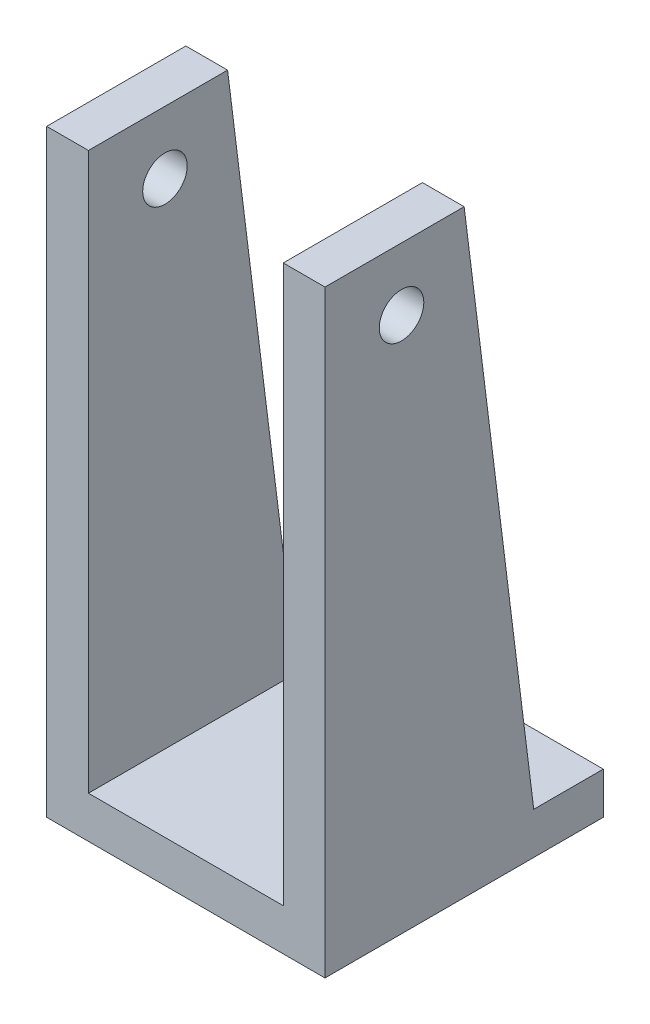
SolidWorks part; units mm, degrees
ref_plane "前视基准面" through (0, 0, 0) normal (0, 0, 1) x (1, 0, 0)
ref_plane "上视基准面" through (0, 0, 0) normal (0, 1, 0) x (1, 0, 0)
ref_plane "右视基准面" through (0, 0, 0) normal (1, 0, 0) x (0, 0, -1)
sketch "草图1" plane through (0, 0, 0) normal (0, 1, 0) x (1, 0, 0)
  line L1 (10, -10) -> (-10, -10)
  line L2 (10, -10) -> (10, 10)
  line L3 (10, 10) -> (-10, 10)
  line L4 (-10, -10) -> (-10, 10)
  point P0 (0, 0)
  dimension "D1" = 20
  dimension "D2" = 20
extrude "凸台-拉伸1" add sketch "草图1" along normal blind 3
sketch "草图4" plane through (-10, 0, 0) normal (-1, 0, 0) x (0, 0, 1)
  line L0 (10, 3) -> (10, 43)
  line L1 (10, 43) -> (0, 43)
  line L2 (0, 43) -> (-5, 3)
  line L3 (-10, 3) -> (10, 3) construction
  line L4 (-5, 3) -> (10, 3)
  dimension "D1" = 40
  dimension "D2" = 15
  dimension "D3" = 10
extrude "凸台-拉伸2" add sketch "草图4" against normal blind 3
sketch "草图5" plane through (10, 0, 0) normal (1, 0, 0) x (0, 0, -1)
  line L0 (-10, 3) -> (5, 3)
  line L1 (5, 3) -> (0, 43)
  line L2 (0, 43) -> (-10, 43)
  line L3 (-10, 43) -> (-10, 3)
extrude "凸台-拉伸3" add sketch "草图5" against normal blind 3
sketch "草图6" plane through (10, 0, 0) normal (1, 0, 0) x (0, 0, -1)
  line L1 (-10, 43) -> (-10, 0) construction
  line L3 (-10, 0) -> (10, 0) construction
  circle A0 centre (-4.5, 38.5) radius 1.6
  dimension "D1" = 38.5
  dimension "D2" = 5.5
extrude "切除-拉伸1" cut sketch "草图6" against normal through all
sketch "草图8" plane through (0, 3, 0) normal (0, 1, 0) x (1, 0, 0)
  line L0 (0, 10) -> (0, -10) construction
  line L1 (10, 10) -> (-10, 10) construction
  line L2 (-7, -10) -> (7, -10) construction
  circle A0 centre (0, 0) radius 2
extrude "切除-拉伸2" cut sketch "草图8" against normal through all
